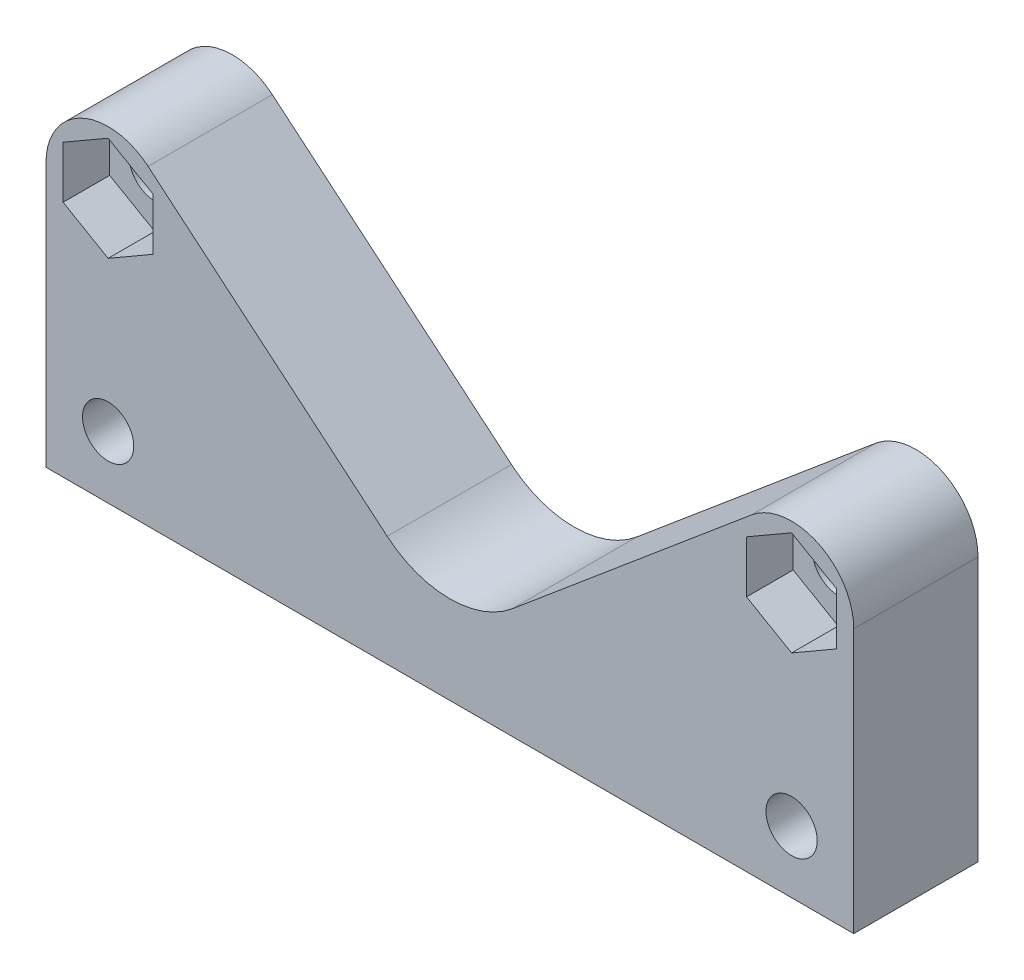
SolidWorks part; units mm, degrees
ref_plane "Front Plane" through (0, 0, 0) normal (0, 0, 1) x (1, 0, 0)
ref_plane "Top Plane" through (0, 0, 0) normal (0, 1, 0) x (1, 0, 0)
ref_plane "Right Plane" through (0, 0, 0) normal (1, 0, 0) x (0, 0, -1)
sketch "Sketch1" plane through (0, 0, 0) normal (0, 0, 1) x (1, 0, 0)
  line L0 (4, 4) -> (48, 4) construction
  line L1 (0, 0) -> (52, 0)
  line L2 (0, 0) -> (0, 17)
  line L3 (4, 17) -> (48, 17) construction
  line L4 (52, 0) -> (52, 17)
  line L5 (48, 4) -> (48, 17) construction
  line L6 (26, 4) -> (26, 11.9438) construction
  line L7 (6.5724, 20.0631) -> (21.9638, 7.1376)
  line L8 (30.0362, 7.1376) -> (45.4276, 20.0631)
  arc A0 (6.5724, 20.0631) -> (0, 17) centre (4, 17) ccw
  arc A1 (45.4276, 20.0631) -> (52, 17) centre (48, 17) cw
  circle A2 centre (4, 17) radius 1.65
  circle A3 centre (48, 17) radius 1.65
  circle A4 centre (4, 4) radius 1.65
  circle A5 centre (48, 4) radius 1.65
  arc A6 (21.9638, 7.1376) -> (30.0362, 7.1376) centre (26, 11.9438) ccw
  dimension "D1" = 4
  dimension "D2" = 4
  dimension "D3" = 3.3
  dimension "D4" = 3.3
  dimension "D5" = 52
  dimension "D6" = 13
  dimension "D7" = 4
extrude "Boss-Extrude1" add sketch "Sketch1" along normal blind 8
sketch "Sketch2" plane through (0, 0, 8) normal (0, 0, 1) x (1, 0, 0)
  line L1 (4, 13.6514) -> (6.9, 15.3257)
  line L2 (6.9, 15.3257) -> (6.9, 18.6743)
  line L3 (6.9, 18.6743) -> (4, 20.3486)
  line L4 (4, 20.3486) -> (1.1, 18.6743)
  line L5 (1.1, 18.6743) -> (1.1, 15.3257)
  line L6 (1.1, 15.3257) -> (4, 13.6514)
  line L7 (48, 13.6514) -> (50.9, 15.3257)
  line L8 (50.9, 15.3257) -> (50.9, 18.6743)
  line L9 (50.9, 18.6743) -> (48, 20.3486)
  line L10 (48, 20.3486) -> (45.1, 18.6743)
  line L11 (45.1, 18.6743) -> (45.1, 15.3257)
  line L12 (45.1, 15.3257) -> (48, 13.6514)
  circle A0 centre (4, 17) radius 2.9 construction
  circle A1 centre (48, 17) radius 2.9 construction
  circle A2 centre (4, 17) radius 1.65 construction
  circle A3 centre (48, 17) radius 1.65 construction
  dimension "D1" = 5.8
extrude "Cut-Extrude1" cut sketch "Sketch2" against normal blind 3
